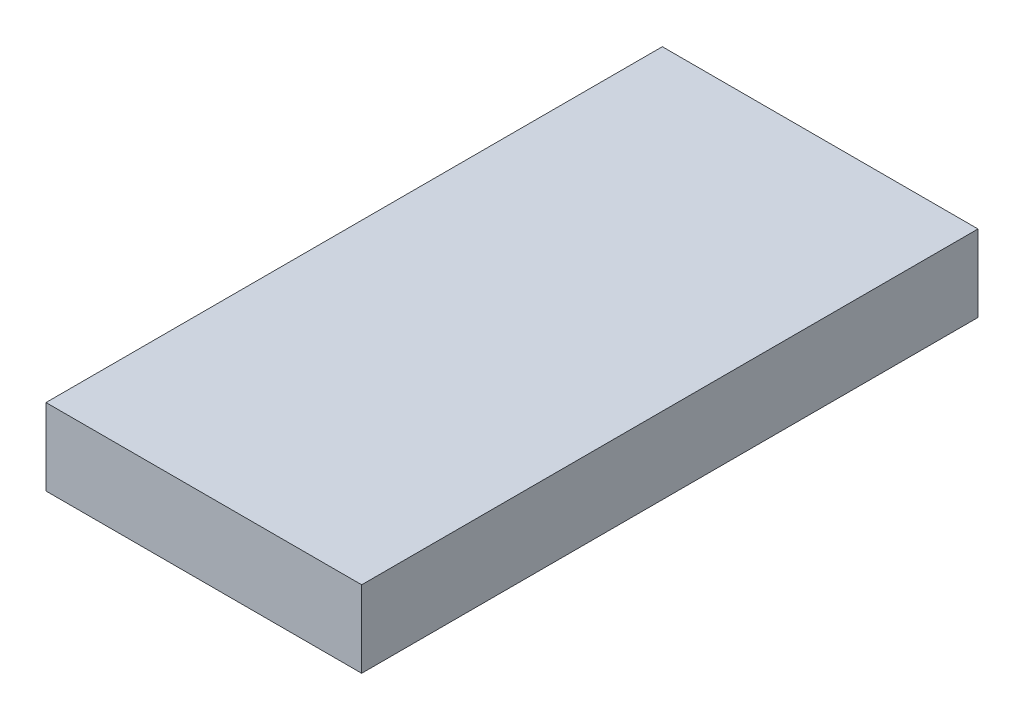
SolidWorks part; units mm, degrees
ref_plane "Front" through (0, 0, 0) normal (0, 0, 1) x (1, 0, 0)
ref_plane "Top" through (0, 0, 0) normal (0, 1, 0) x (1, 0, 0)
ref_plane "Right" through (0, 0, 0) normal (1, 0, 0) x (0, 0, -1)
sketch "Sketch1" plane through (0, 0, 0) normal (0, 1, 0) x (1, 0, 0)
  line L1 (10.5, -20.5) -> (-10.5, -20.5)
  line L2 (10.5, -20.5) -> (10.5, 20.5)
  line L3 (10.5, 20.5) -> (-10.5, 20.5)
  line L4 (-10.5, -20.5) -> (-10.5, 20.5)
  line L5 (10.5, -20.5) -> (-10.5, 20.5) construction
  line L6 (10.5, 20.5) -> (-10.5, -20.5) construction
  point P0 (0, 0)
  dimension "D1" = 41
  dimension "D2" = 21
extrude "Boss-Extrude1" add sketch "Sketch1" along normal blind 5.1
